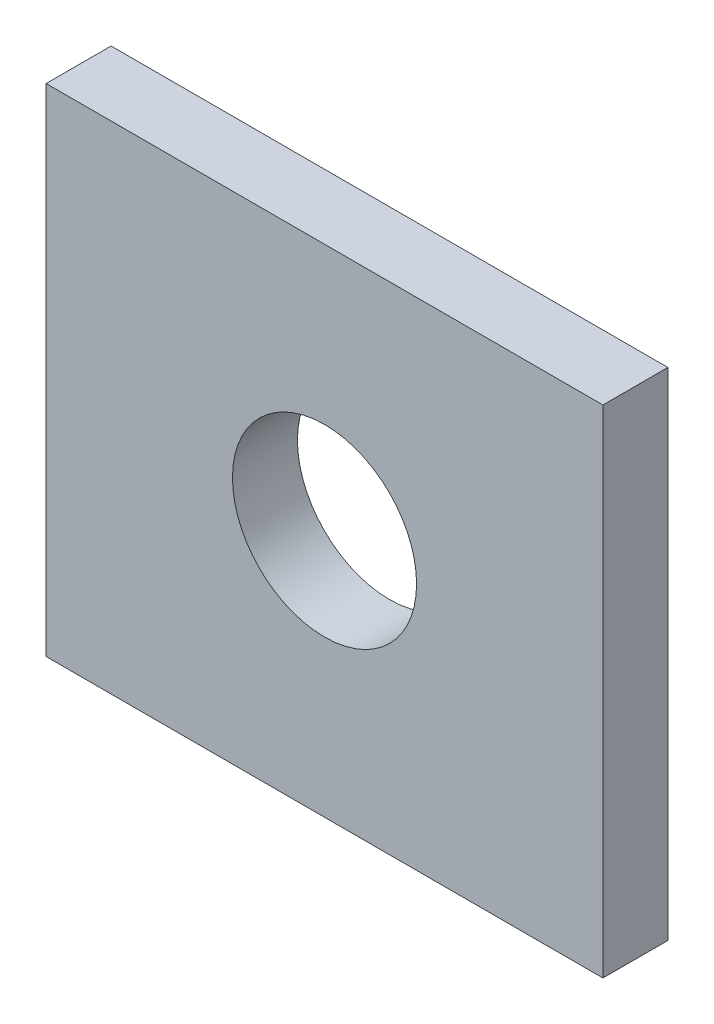
SolidWorks part; units mm, degrees
material "Plain Carbon Steel"
ref_plane "Front Plane" through (0, 0, 0) normal (0, 0, 1) x (1, 0, 0)
ref_plane "Top Plane" through (0, 0, 0) normal (0, 1, 0) x (1, 0, 0)
ref_plane "Right Plane" through (0, 0, 0) normal (1, 0, 0) x (0, 0, -1)
sketch "Sketch1" plane through (0, 0, 0) normal (0, 0, 1) x (1, 0, 0)
  line L1 (0, 0) -> (54, 0)
  line L2 (0, 0) -> (0, 48.13)
  line L3 (0, 48.13) -> (54, 48.13)
  line L4 (54, 0) -> (54, 48.13)
  dimension "D1" = 48.13
  dimension "D2" = 54
extrude "Boss-Extrude1" add sketch "Sketch1" along normal blind 6.3
sketch "Sketch2" plane through (0, 0, 6.3) normal (0, 0, 1) x (1, 0, 0)
  line L0 (0, 48.13) -> (0, 0) construction
  line L1 (54, 48.13) -> (0, 48.13) construction
  circle A0 centre (27, 24.065) radius 8.9281
  point P4 (0, 24.065)
  point P7 (27, 48.13)
  dimension "D1" = 17.8562
extrude "Cut-Extrude1" cut sketch "Sketch2" against normal through all
